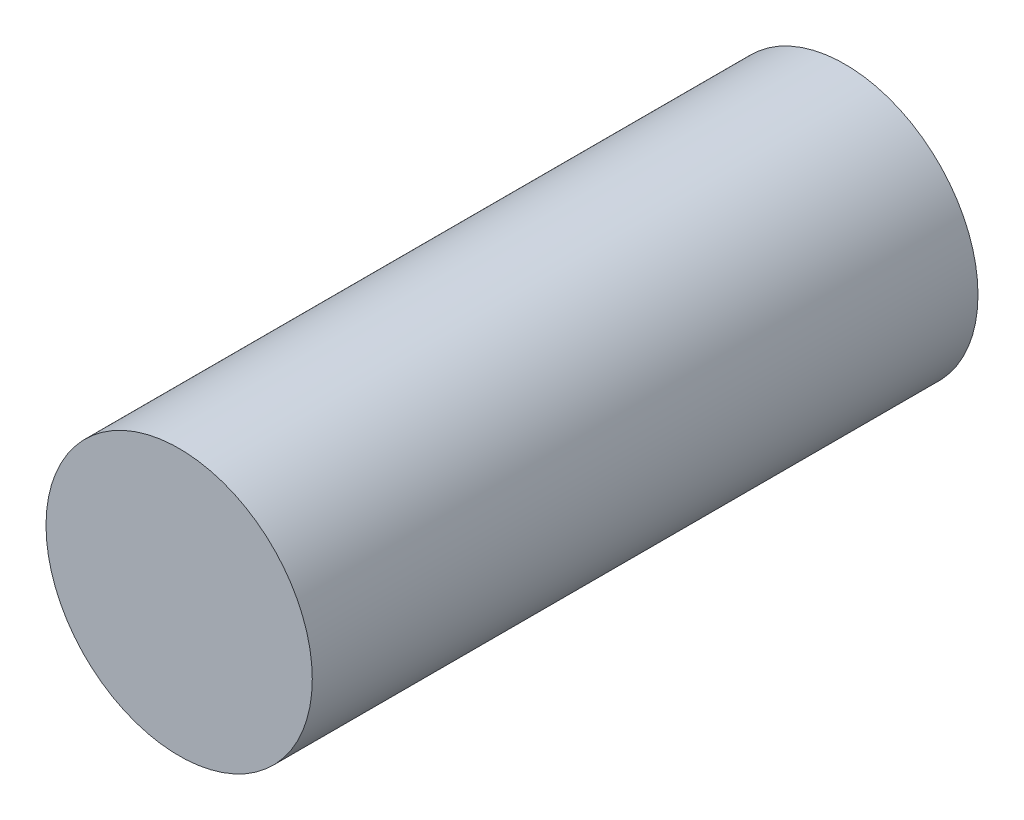
SolidWorks part; units mm, degrees
ref_plane "Front Plane" through (0, 0, 0) normal (0, 0, 1) x (1, 0, 0)
ref_plane "Top Plane" through (0, 0, 0) normal (0, 1, 0) x (1, 0, 0)
ref_plane "Right Plane" through (0, 0, 0) normal (1, 0, 0) x (0, 0, -1)
sketch "Sketch1" plane through (0, 0, 0) normal (0, 0, 1) x (1, 0, 0)
  circle A0 centre (0, 0) radius 6
  dimension "D1" = 12
extrude "Boss-Extrude1" add sketch "Sketch1" along normal blind 30
